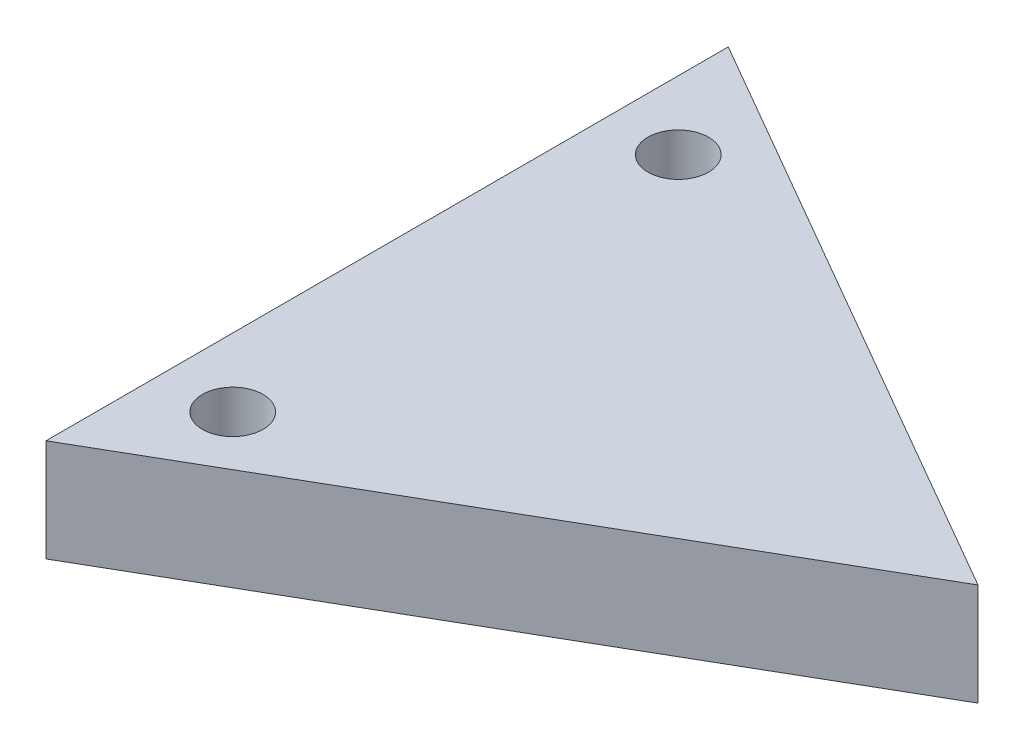
SolidWorks part; units mm, degrees
ref_plane "Front" through (0, 0, 0) normal (0, 0, 1) x (1, 0, 0)
ref_plane "Top" through (0, 0, 0) normal (0, 1, 0) x (1, 0, 0)
ref_plane "Right" through (0, 0, 0) normal (1, 0, 0) x (0, 0, -1)
sketch "Sketch1" plane through (0, 0, 0) normal (0, 1, 0) x (1, 0, 0)
  line L1 (11.547, 0) -> (-5.7735, 10)
  line L2 (-5.7735, 10) -> (-5.7735, -10)
  line L3 (-5.7735, -10) -> (11.547, 0)
  circle A0 centre (0, 0) radius 5.7735 construction
  dimension "D1" = 20
  dimension "D2" = 20
  dimension "D3" = 20
extrude "Extrude1" add sketch "Sketch1" along normal blind 3
sketch "Sketch2" plane through (0, 3, 0) normal (0, 1, 0) x (-1, 0, 0)
  line L0 (-14.794, 0) -> (12.5348, 0) construction
  line L1 (0, -13.2507) -> (0, 13.7519) construction
hole_wizard "#2-56 Tapped Hole1" positions "3DSketch3" profile "Sketch6" tap size "#2-56" standard "Ansi Inch"
sketch3d "3DSketch3"
  line L1 (14.794, 3, 0) -> (-12.5348, 3, 0) construction
  line L2 (0, 3, -13.2507) -> (0, 3, 13.7519) construction
  point P6 (-3.77, 3, -6.53)
  dimension "D1" = 6.53
  dimension "D2" = 3.77
sketch "Sketch6" plane through (-3.77, 3, -6.53) normal (1, 0, 0) x (0, 0, 1)
  line L0 (0, 0) -> (0, 7.1742)
  line L1 (0, 7.1742) -> (0.889, 6.64)
  line L2 (0.889, 6.64) -> (0.889, 0)
  line L5 (0.889, 0) -> (0, 0)
  line L10 (0, 7.1742) -> (-0.889, 6.64) construction
  line L11 (0, -6.35) -> (0, 107.95) construction
  dimension "Tap Drill Dia." = 1.778
  dimension "Tap Drill Depth" = 6.64
  dimension "Drill Angle" = 118
pattern_linear "LPattern1" count 2 spacing 13.06 along (0, 0, 1) of "#2-56 Tapped Hole1"
sketch "Sketch9" plane through (0, 3, 0) normal (0, 1, 0) x (-1, 0, 0)
  line L0 (-14.794, 0) -> (12.5348, 0) construction
  line L1 (0, -13.2507) -> (0, 13.7519) construction
  point P0 (2.31, -4)
  point P5 (2.31, 4)
  point P6 (-4.62, 0)
  point P7 (0, 0)
  dimension "D1" = 4
  dimension "D2" = 2.31
  dimension "D3" = 4
  dimension "D4" = 2.31
  dimension "D5" = 4.62
